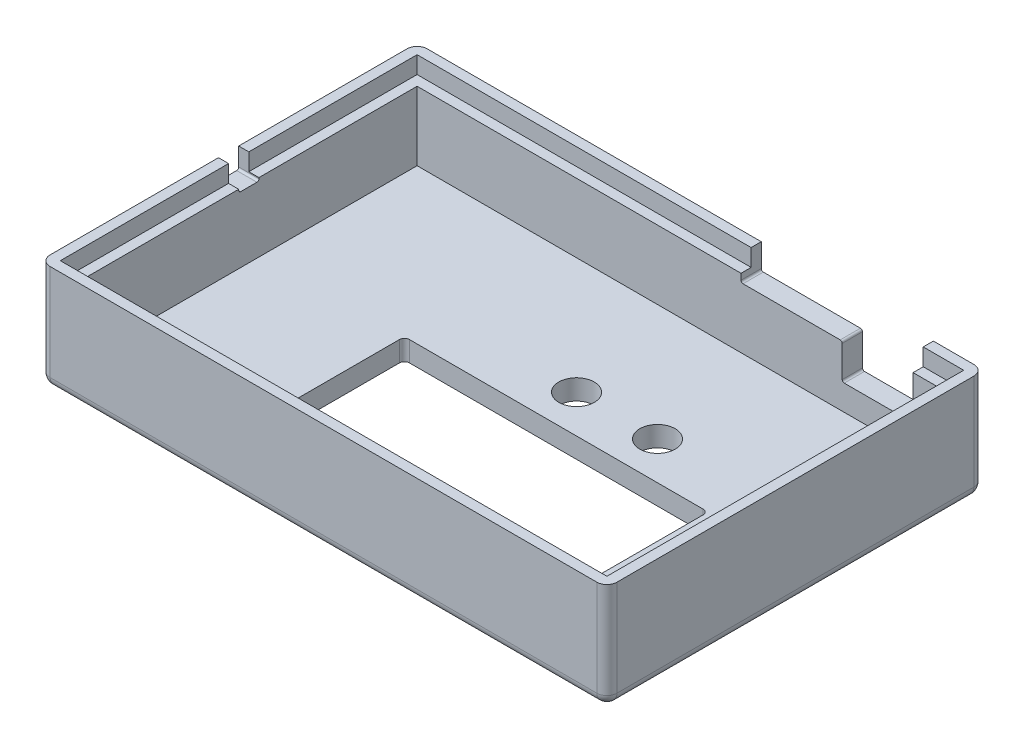
SolidWorks part; units mm, degrees
ref_plane "Front Plane" through (0, 0, 0) normal (0, 0, 1) x (1, 0, 0)
ref_plane "Top Plane" through (0, 0, 0) normal (0, 1, 0) x (1, 0, 0)
ref_plane "Right Plane" through (0, 0, 0) normal (1, 0, 0) x (0, 0, -1)
sketch "Sketch1" plane through (0, 0, 0) normal (0, 1, 0) x (1, 0, 0)
  line L0 (0, 0) -> (56, 0)
  line L1 (56, 0) -> (56, 37.25)
  line L2 (56, 37.25) -> (0, 37.25)
  line L3 (0, 37.25) -> (0, 0)
  dimension "D1" = 56
  dimension "D2" = 37.25
extrude "Boss-Extrude1" add sketch "Sketch1" along normal blind 2
sketch "Sketch2" plane through (0, 2, 0) normal (0, 1, 0) x (1, 0, 0)
  line L0 (2, 35.25) -> (2, 2)
  line L1 (2, 2) -> (54, 2)
  line L2 (0, 37.25) -> (0, 0) construction
  line L3 (0, 0) -> (56, 0) construction
  line L4 (2, 35.25) -> (54, 35.25)
  line L5 (54, 35.25) -> (54, 2)
  line L6 (56, 0) -> (56, 37.25) construction
  line L7 (56, 37.25) -> (0, 37.25) construction
  line L12 (0, 37.25) -> (0, 0)
  line L13 (0, 0) -> (56, 0)
  line L14 (56, 0) -> (56, 37.25)
  line L15 (56, 37.25) -> (0, 37.25)
  line L16 (0, 37.25) -> (0, 0)
  line L17 (0, 0) -> (56, 0)
  line L18 (56, 0) -> (56, 37.25)
  line L19 (56, 37.25) -> (0, 37.25)
  dimension "D1" = 2
  dimension "D2" = 2
  dimension "D3" = 2
  dimension "D4" = 2
  dimension "D5" = 0
extrude "Boss-Extrude2" add sketch "Sketch2" along normal blind 8.5
sketch "Sketch3" plane through (0, 2, 0) normal (0, 1, 0) x (1, 0, 0)
  line L0 (54, 2) -> (54, 35.25) construction
  line L4 (2, 18.625) -> (54, 18.625) construction
  line L5 (2, 35.25) -> (2, 2) construction
  line L6 (12, 6) -> (48, 6) construction
  line L7 (12, 32) -> (12, 6) construction
  circle A0 centre (12, 32) radius 1.6
  circle A1 centre (12, 6) radius 1.6
  circle A2 centre (48, 6) radius 1.6
  circle A6 centre (48, 6) radius 1.5 construction
  circle A7 centre (12, 6) radius 1.5 construction
  circle A8 centre (12, 32) radius 1.5 construction
  circle A9 centre (48, 6) radius 2 construction
  circle A10 centre (12, 6) radius 2 construction
  circle A11 centre (12, 32) radius 2 construction
sketch "Sketch5" plane through (0, 10.5, 0) normal (0, 1, 0) x (1, 0, 0)
  line L0 (1, 1) -> (55, 1)
  line L1 (0, 0) -> (56, 0) construction
  line L2 (55, 1) -> (55, 36.25)
  line L3 (55, 36.25) -> (1, 36.25)
  line L4 (1, 36.25) -> (1, 1)
  line L5 (56, 0) -> (56, 37.25) construction
  line L6 (56, 37.25) -> (0, 37.25) construction
  line L7 (0, 37.25) -> (0, 0) construction
  line L8 (0, 37.25) -> (0, 0)
  line L9 (56, 37.25) -> (0, 37.25)
  line L10 (56, 0) -> (56, 37.25)
  line L11 (0, 0) -> (56, 0)
  line L12 (54, 2) -> (54, 35.25) construction
  line L13 (54, 35.25) -> (2, 35.25) construction
  line L14 (2, 35.25) -> (2, 2) construction
  line L15 (2, 2) -> (54, 2) construction
  line L16 (54, 2) -> (54, 35.25)
  line L17 (54, 35.25) -> (2, 35.25)
  line L18 (2, 35.25) -> (2, 2)
  line L19 (2, 2) -> (54, 2)
  line M9 (2, 2) -> (2, 35.25)
  line M10 (2, 35.25) -> (54, 35.25)
  line M11 (54, 35.25) -> (54, 2)
  line M12 (54, 2) -> (2, 2)
  dimension "D1" = 1
  dimension "D2" = 1
  dimension "D3" = 1
  dimension "D4" = 1
extrude "Cut-Extrude1" cut sketch "Sketch5" against normal blind 1 contours L3 L4 L0 L2 M12 M9 M10 M11 | L18 L19 L16 L17
fillet "Fillet1" radius 1 4 edges at (56, 5.25, -37.25) (56, 5.25, 0) (0, 5.25, -37.25) (0, 5.25, 0)
extrude "Cut-Extrude2" [suppressed] cut sketch "Sketch3" against normal blind 10
sketch "Sketch7" plane through (0, 2, 0) normal (0, 1, 0) x (1, 0, 0)
  line L0 (16, 6) -> (46, 6)
  line L1 (46, 6) -> (46, 20)
  line L2 (16, 6) -> (16, 20)
  line L3 (16, 20) -> (46, 20)
  line L4 (54, 2) -> (54, 35.25) construction
  line L6 (2, 2) -> (54, 2) construction
  dimension "D1" = 14
  dimension "D2" = 30
  dimension "D3" = 8
  dimension "D4" = 4
extrude "Cut-Extrude3" cut sketch "Sketch7" against normal blind 10
sketch "Sketch8" plane through (0, 0, 0) normal (0, -1, 0) x (1, 0, 0)
  circle A0 centre (29.25, -23.75) radius 1.75
  circle A1 centre (37.25, -23.75) radius 1.75
extrude "Cut-Extrude4" cut sketch "Sketch8" against normal blind 10
sketch "Sketch9" plane through (0, 0, -37.25) normal (0, 0, -1) x (-1, 0, 0)
  line L0 (-44, 4.5) -> (-44, 10.5)
  line L1 (-44, 10.5) -> (-51, 10.5)
  line L2 (-51, 10.5) -> (-51, 4.5)
  line L3 (-51, 4.5) -> (-44, 4.5)
  line L4 (-55, 10.5) -> (-55, 0) construction
  line L5 (-55, 10.5) -> (-1, 10.5) construction
  point P5 (-55, 5.25)
  dimension "D1" = 7
  dimension "D2" = 6
  dimension "D3" = 4
  dimension "D4" = 0
extrude "Cut-Extrude5" cut sketch "Sketch9" against normal blind 3
sketch "Sketch10" plane through (0, 0, -37.25) normal (0, 0, -1) x (-1, 0, 0)
  line L0 (-44, 10.5) -> (-44, 8)
  line L1 (-55, 10.5) -> (-51, 10.5) construction
  line L2 (-44, 8) -> (-34, 8)
  line L3 (-34, 8) -> (-34, 10.5)
  line L4 (-55, 10.5) -> (-55, 0) construction
  line L5 (-34, 10.5) -> (-44, 10.5)
  dimension "D1" = 10
  dimension "D2" = 2.5
  dimension "D3" = 11
extrude "Cut-Extrude6" cut sketch "Sketch10" against normal blind 3
fillet "Fillet2" radius 0.5 4 edges at (46, 1, -20) (16, 1, -20) (16, 1, -6) (46, 1, -6)
sketch "Sketch11" plane through (0, 0, 0) normal (0, -1, 0) x (1, 0, 0)
  line L0 (0, -24.271) -> (14, -24.271)
  line L1 (0, -36.25) -> (0, -1) construction
  line L2 (14, -24.271) -> (14, -14.271)
  line L3 (14, -14.271) -> (0, -14.271)
  line L4 (0, -14.271) -> (0, -24.271)
  line L5 (1, 0) -> (55, 0) construction
  dimension "D1" = 14
  dimension "D2" = 10
  dimension "D3" = 14.271
extrude "Cut-Extrude7" [suppressed] cut sketch "Sketch11" against normal through all
fillet "Fillet3" radius 1 8 edges at (0, 0, -18.625) (0.2929, 0, -0.2929) (28, 0, 0) (55.7071, 0, -0.2929) (56, 0, -18.625) (55.7071, 0, -36.9571) (0.2929, 0, -36.9571) (28, 0, -37.25)
fillet "Fillet4" [suppressed] radius 0.5
fillet "Fillet5" radius 0.2 4 edges at (34, 8, -36.25) (44, 8, -36.25) (51, 4.5, -36.25) (44, 4.5, -36.25)
sketch "Sketch12" plane through (0, 9.5, 0) normal (0, 1, 0) x (1, 0, 0)
  line L12 (34, 35.25) -> (34, 36.25)
  line L13 (34, 36.25) -> (1, 36.25)
  line L14 (1, 36.25) -> (1, 1)
  line L15 (1, 1) -> (55, 1)
  line L16 (55, 1) -> (55, 36.25)
  line L17 (55, 36.25) -> (51, 36.25)
  line L18 (51, 36.25) -> (51, 35.25)
  line L19 (51, 35.25) -> (54, 35.25)
  line L20 (54, 35.25) -> (54, 2)
  line L21 (54, 2) -> (2, 2)
  line L22 (2, 2) -> (2, 35.25)
  line L23 (2, 35.25) -> (34, 35.25)
  line L24 (34, 35.25) -> (34, 36.25)
  line L25 (34, 36.25) -> (1, 36.25)
  line L26 (1, 36.25) -> (1, 1)
  line L27 (1, 1) -> (55, 1)
  line L28 (55, 1) -> (55, 36.25)
  line L29 (55, 36.25) -> (51, 36.25)
  line L30 (51, 36.25) -> (51, 35.25)
  line L31 (51, 35.25) -> (54, 35.25)
  line L32 (54, 35.25) -> (54, 2)
  line L33 (54, 2) -> (2, 2)
  line L34 (2, 2) -> (2, 35.25)
  line L35 (2, 35.25) -> (34, 35.25)
  point P12 (0, 0)
  point P17 (0, 0)
  point P18 (0, 0)
  dimension "D1" = 0
extrude "Cut-Extrude8" cut sketch "Sketch12" against normal blind 0.7
sketch "Sketch13" plane through (0, 0, 0) normal (-1, 0, 0) x (0, 0, 1)
  line L0 (-18.625, 10.5) -> (-18.625, 8.5) construction
  line L1 (-36.25, 10.5) -> (-1, 10.5) construction
  line L2 (-18.625, 8.5) -> (-19.625, 8.5)
  line L3 (-19.625, 8.5) -> (-19.625, 10.5)
  line L4 (-18.625, 8.5) -> (-17.625, 8.5)
  line L5 (-17.625, 8.5) -> (-17.625, 10.5)
  line L6 (-19.625, 10.5) -> (-17.625, 10.5)
  point P9 (0, 0)
  dimension "D1" = 2
  dimension "D2" = 1
  dimension "D3" = 2
extrude "Cut-Extrude10" cut sketch "Sketch13" against normal blind 5
fillet "Fillet6" radius 0.2 2 edges at (1, 8.5, -19.625) (1, 8.5, -17.625)
